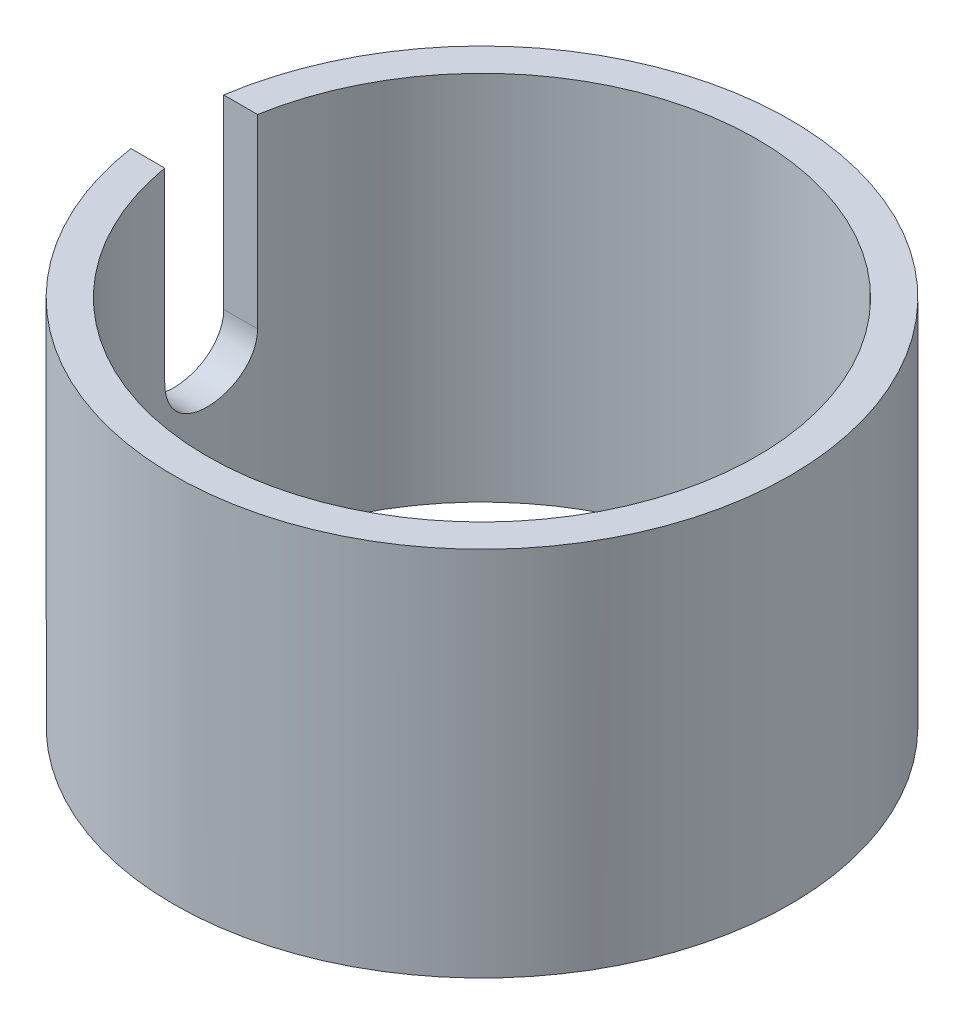
SolidWorks part; units mm, degrees
ref_plane "Front Plane" through (0, 0, 0) normal (0, 0, 1) x (1, 0, 0)
ref_plane "Top Plane" through (0, 0, 0) normal (0, 1, 0) x (1, 0, 0)
ref_plane "Right Plane" through (0, 0, 0) normal (1, 0, 0) x (0, 0, -1)
sketch "Sketch1" plane through (0, 0, 0) normal (0, 1, 0) x (1, 0, 0)
  circle A0 centre (0, 0) radius 10.541
  circle A1 centre (0, 0) radius 9.398
  dimension "D1" = 18.796
  dimension "D2" = 21.082
extrude "Boss-Extrude1" add sketch "Sketch1" along normal blind 12.7 contours A0 A1
sketch "Sketch2" plane through (0, 0, 0) normal (1, 0, 0) x (0, 0, -1)
  line L0 (-1.5875, 12.7) -> (1.5875, 12.7)
  line L1 (9.398, 12.7) -> (-9.398, 12.7) construction
  line L2 (1.5875, 12.7) -> (1.5875, 6.35)
  line L3 (-1.5875, 12.7) -> (-1.5875, 6.35)
  arc A0 (1.5875, 6.35) -> (-1.5875, 6.35) centre (0, 6.35) cw
  point P6 (1.2994, 4.4681)
  point P8 (0, 0)
  dimension "D1" = 3.175
  dimension "D2" = 6.35
extrude "Cut-Extrude1" cut sketch "Sketch2" against normal blind 12.7 contours L2 A0 L3 L0
